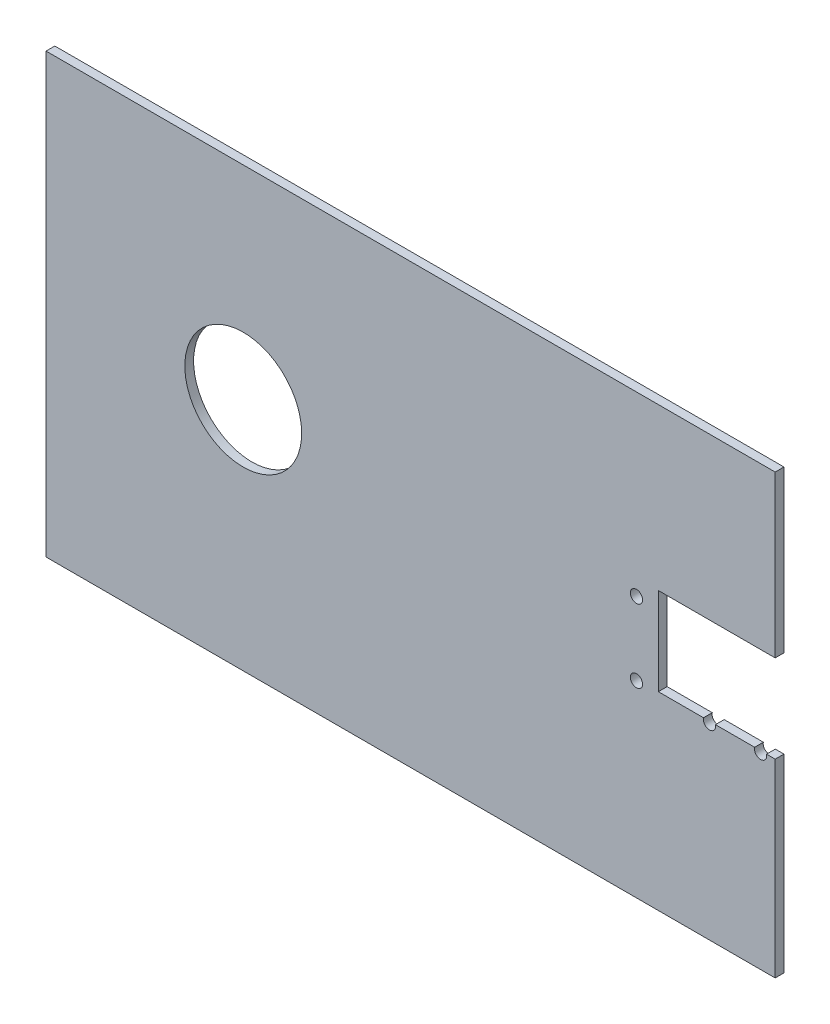
SolidWorks part; units mm, degrees
ref_plane "Front Plane" through (0, 0, 0) normal (0, 0, 1) x (1, 0, 0)
ref_plane "Top Plane" through (0, 0, 0) normal (0, 1, 0) x (1, 0, 0)
ref_plane "Right Plane" through (0, 0, 0) normal (1, 0, 0) x (0, 0, -1)
sketch "Sketch1" plane through (0, 0, 0) normal (0, 0, 1) x (1, 0, 0)
  line L1 (0, 0) -> (249.6, 0)
  line L2 (0, 0) -> (0, -150)
  line L3 (0, -150) -> (249.6, -150)
  line L4 (249.6, 0) -> (249.6, -150)
  dimension "D1" = 150
  dimension "D2" = 249.6
extrude "Boss-Extrude1" add sketch "Sketch1" along normal blind 3
sketch "Sketch2" plane through (0, 0, 3) normal (0, 0, 1) x (1, 0, 0)
  circle A0 centre (67.5, -69.5849) radius 20
  dimension "D1" = 40
extrude "Cut-Extrude1" cut sketch "Sketch2" against normal through all
sketch "Sketch3" plane through (0, 0, 3) normal (0, 0, 1) x (1, 0, 0)
  line L0 (249.6, -55.1137) -> (195.8, -55.1137) construction
  line L1 (209.6, -55.1137) -> (249.6, -55.1137)
  line L2 (209.6, -55.1137) -> (209.6, -85.1137)
  line L3 (209.6, -85.1137) -> (249.6, -85.1137)
  line L4 (249.6, -55.1137) -> (249.6, -85.1137)
  line L5 (249.6, -150) -> (249.6, 0) construction
  dimension "D1" = 30
  dimension "D2" = 40
extrude "Cut-Extrude2" cut sketch "Sketch3" against normal blind 5
sketch "Sketch4" plane through (0, 0, 3) normal (0, 0, 1) x (1, 0, 0)
  circle A0 centre (244.6, -85.6137) radius 2.1
  circle A1 centre (227.1, -85.6137) radius 2.1
  circle A2 centre (239.6, -73.1137) radius 4
  circle A3 centre (244.6, -60.6137) radius 2.1
  circle A4 centre (227.1, -60.6137) radius 2.1
  circle A5 centre (202.1, -85.6137) radius 2.1
  circle A8 centre (202.1, -60.6137) radius 2.1
  circle A9 centre (244.6, -85.6137) radius 2.1 construction
  circle A10 centre (239.6, -73.1137) radius 4 construction
  circle A11 centre (227.1, -85.6137) radius 2.1 construction
  circle A12 centre (202.1, -60.6137) radius 2.1 construction
  circle A13 centre (227.1, -60.6137) radius 2.1 construction
  circle A14 centre (202.1, -85.6137) radius 2.1 construction
  circle A16 centre (214.6, -73.1137) radius 4
  circle A17 centre (214.6, -73.1137) radius 4 construction
  circle A18 centre (244.6, -60.6137) radius 2.1 construction
extrude "Cut-Extrude3" cut sketch "Sketch4" against normal through all
